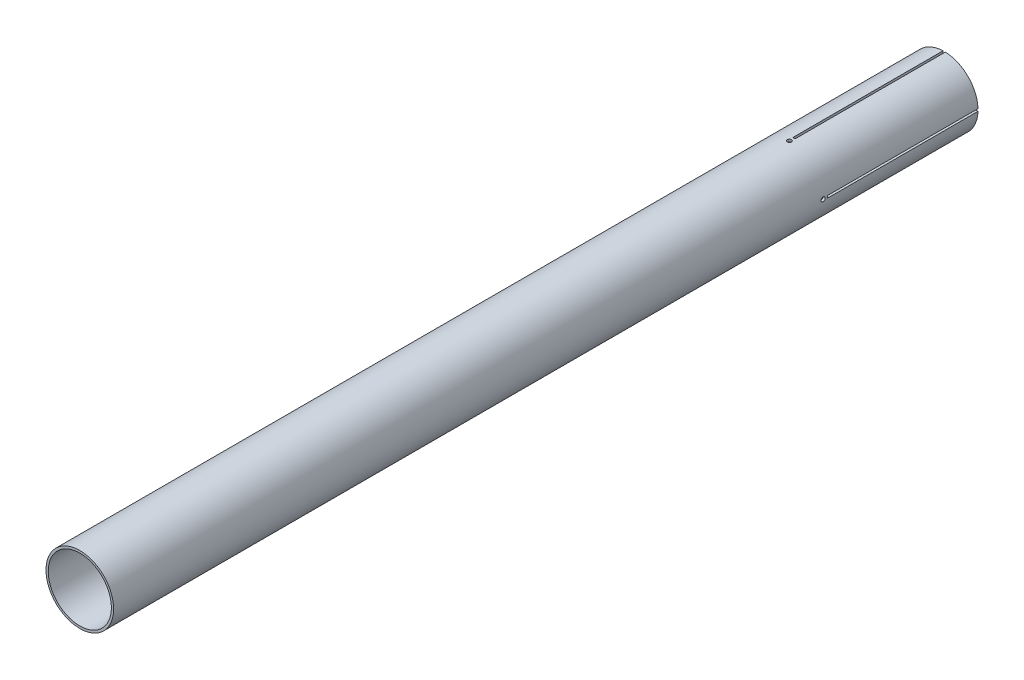
SolidWorks part; units mm, degrees
ref_plane "Plan de face" through (0, 0, 0) normal (0, 0, 1) x (1, 0, 0)
ref_plane "Plan de dessus" through (0, 0, 0) normal (0, 1, 0) x (1, 0, 0)
ref_plane "Plan de droite" through (0, 0, 0) normal (1, 0, 0) x (0, 0, -1)
sketch "Esquisse1" plane through (0, 0, 0) normal (0, 0, 1) x (1, 0, 0)
  circle A0 centre (0, 0) radius 45
  dimension "D1" = 90
extrude "Boss.-Extru.1" add sketch "Esquisse1" along normal blind 1150
sketch "Esquisse2" plane through (0, 0, 0) normal (0, 0, -1) x (-1, 0, 0)
  circle A0 centre (0, 0) radius 42
  dimension "D1" = 84
extrude "Enlèv. mat.-Extru.1" cut sketch "Esquisse2" against normal blind 1150
sketch "Esquisse3" plane through (0, 0, 0) normal (0, 0, 1) x (1, 0, 0)
  line L0 (-12.1391, 0) -> (-67.8609, 0) construction
  line L1 (-50, 1.5) -> (-40, 1.5)
  line L2 (-50, 1.5) -> (-50, -1.5)
  line L3 (-50, -1.5) -> (-40, -1.5)
  line L4 (-40, 1.5) -> (-40, -1.5)
  point P8 (-40, 0)
  dimension "D1" = 3
  dimension "D2" = 10
  dimension "D3" = 40
extrude "Enlèv. mat.-Extru.2" cut sketch "Esquisse3" along normal blind 200
pattern_circular "Répétition circulaire1" count 4 over 360 about axis through (0, 0, 0) along (0, 0, 1) of "Enlèv. mat.-Extru.2"
sketch "Esquisse4" plane through (0, 0, 0) normal (0, 0, -1) x (-1, 0, 0)
  line L0 (0, 0) -> (106.8908, 0) construction
hole_wizard "Dégagement M51" positions "Esquisse3D1" profile "Esquisse5" hole size "M5" standard "ISO" end condition through all
sketch3d "Esquisse3D1"
  line L7 (-45, 0, 0) -> (-45, 0, 412) construction
  line L8 (0, 0, 0) -> (-106.8908, 0, 0) construction
  point P0 (-45, 0, 206)
  point P39 (-95.9154, -60.149, 0)
  dimension "D1" = 206
sketch "Esquisse5" plane through (-45, 0, 206) normal (0, 1, 0) x (0, 0, 1)
  line L0 (0, 0) -> (0, 90)
  line L1 (0, 90) -> (2.75, 90)
  line L2 (2.75, 90) -> (2.75, 0)
  line L5 (2.75, 0) -> (0, 0)
  line L11 (0, -6.35) -> (0, 107.95) construction
  dimension "Diamètre du perçage jusqu'au prochain" = 5.5
  dimension "Profondeur du perçage jusqu'au prochain" = 90
pattern_circular "Répétition circulaire2" count 2 over 90 about axis through (0, 0, 0) along (0, 0, 1) of "Dégagement M51"
